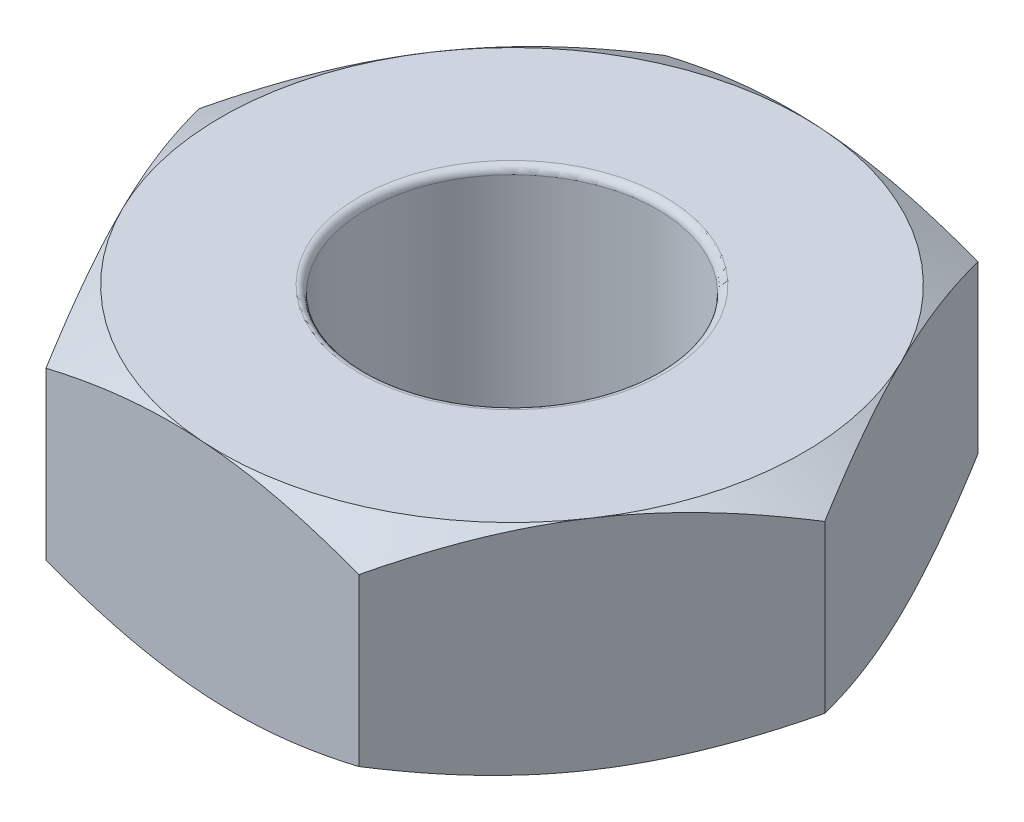
SolidWorks part; units mm, degrees
ref_plane "Front Plane" through (0, 0, 0) normal (0, 0, 1) x (1, 0, 0)
ref_plane "Top Plane" through (0, 0, 0) normal (0, 1, 0) x (1, 0, 0)
ref_plane "Right Plane" through (0, 0, 0) normal (1, 0, 0) x (0, 0, -1)
sketch "Sketch1" plane through (0, 0, 0) normal (0, 1, 0) x (1, 0, 0)
  line L1 (-2.3043, 0.1539) -> (-1.2854, -1.9186)
  line L2 (-1.2854, -1.9186) -> (1.0189, -2.0725)
  line L3 (1.0189, -2.0725) -> (2.3043, -0.1539)
  line L4 (2.3043, -0.1539) -> (1.2854, 1.9186)
  line L5 (1.2854, 1.9186) -> (-1.0189, 2.0725)
  line L6 (-1.0189, 2.0725) -> (-2.3043, 0.1539)
  circle A0 centre (0, 0) radius 2 construction
  circle A1 centre (0, 0) radius 1
  dimension "D1" = 4
  dimension "D2" = 2
extrude "Boss-Extrude1" add sketch "Sketch1" along normal blind 1.5
sketch "Sketch2" plane through (0, 1.5, 0) normal (0, 1, 0) x (1, 0, 0)
  circle A0 centre (0, 0) radius 2 construction
  circle A1 centre (0, 0) radius 2
extrude "Cut-Extrude1" cut sketch "Sketch2" against normal blind 2 draft 60 flip side to cut
sketch "Sketch3" plane through (0, 0, 0) normal (0, -1, 0) x (1, 0, 0)
  circle A0 centre (0, 0) radius 2 construction
  circle A1 centre (0, 0) radius 2
extrude "Cut-Extrude2" cut sketch "Sketch3" against normal blind 2 draft 60 flip side to cut
fillet "Fillet1" radius 0.05 2 edges at (0, 0, 1) (0, 1.5, 1)
